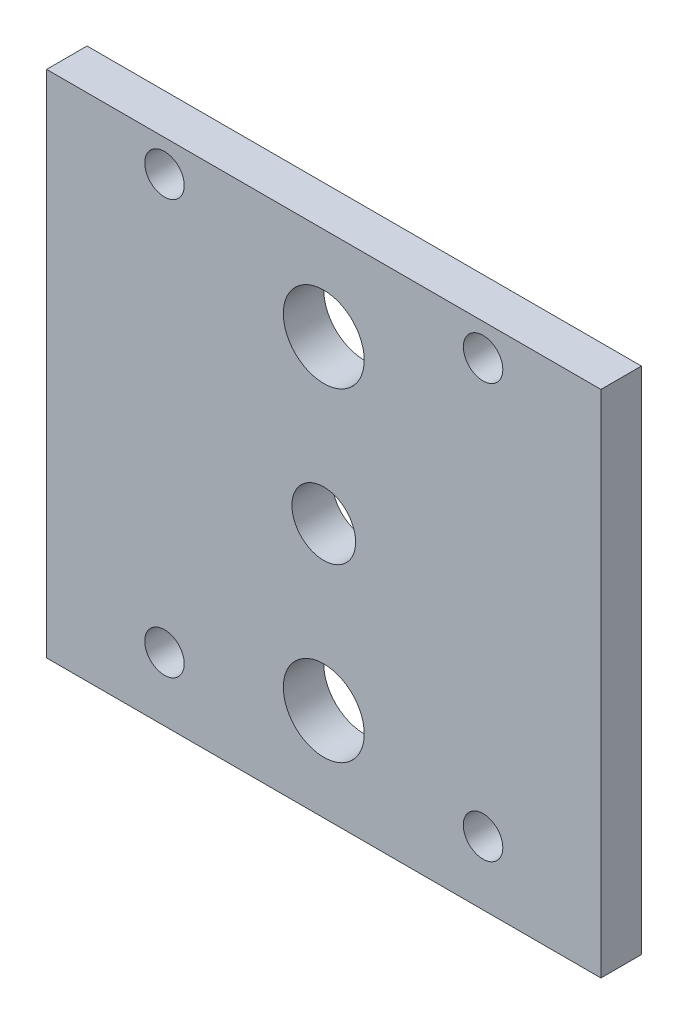
SolidWorks part; units mm, degrees
ref_plane "Front" through (0, 0, 0) normal (0, 0, 1) x (1, 0, 0)
ref_plane "Top" through (0, 0, 0) normal (0, 1, 0) x (1, 0, 0)
ref_plane "Right" through (0, 0, 0) normal (1, 0, 0) x (0, 0, -1)
sketch "Croquis1" plane through (0, 0, 0) normal (0, 0, 1) x (1, 0, 0)
  line L0 (0, 40) -> (0, -40) construction
  line L1 (-43.5, 40) -> (43.5, 40)
  line L2 (-43.5, 40) -> (-43.5, -40)
  line L3 (-43.5, -40) -> (43.5, -40)
  line L4 (43.5, 40) -> (43.5, -40)
  line L5 (-43.5, 40) -> (43.5, -40) construction
  line L6 (-43.5, -40) -> (43.5, 40) construction
  line L7 (43.5, 0) -> (-43.5, 0) construction
  line L8 (-25, 35) -> (25, 35) construction
  line L9 (25, 35) -> (25, -30) construction
  line L10 (25, -30) -> (-25, -30) construction
  line L11 (-25, -30) -> (-25, 35) construction
  circle A0 centre (-25, 35) radius 3.1
  circle A1 centre (25, 35) radius 3.1
  circle A2 centre (0, 25.4) radius 6.35
  circle A3 centre (0, -25.4) radius 6.35
  circle A4 centre (-25, -30) radius 3.1
  circle A5 centre (25, -30) radius 3.1
  circle A6 centre (0, 0) radius 5
  point P0 (0, 0)
  dimension "D5" = 6.2
  dimension "D6" = 6.2
  dimension "D7" = 6.2
  dimension "D8" = 6.2
  dimension "D11" = 12.7
  dimension "D12" = 12.7
  dimension "D15" = 10
  dimension "D1" = 87
  dimension "D2" = 80
  dimension "D3" = 50
  dimension "D4" = 65
  dimension "D9" = 25
  dimension "D10" = 35
  dimension "D13" = 50.8
  dimension "D14" = 25.4
extrude "Saliente-Extruir1" add sketch "Croquis1" along normal blind 6.35
